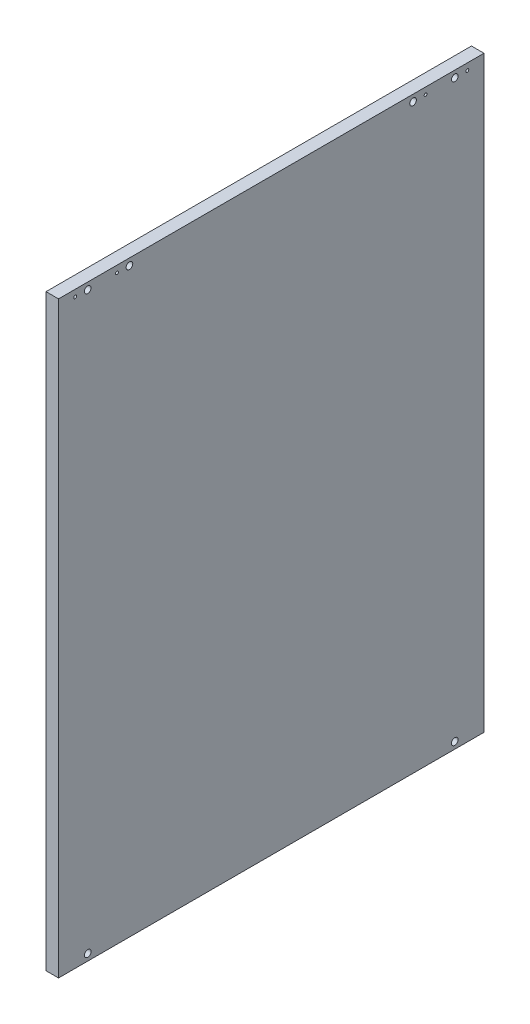
SolidWorks part; units mm, degrees
material "Pine"
ref_plane "Front Plane" through (0, 0, 0) normal (0, 0, 1) x (1, 0, 0)
ref_plane "Top Plane" through (0, 0, 0) normal (0, 1, 0) x (1, 0, 0)
ref_plane "Right Plane" through (0, 0, 0) normal (1, 0, 0) x (0, 0, -1)
sketch "Эскиз1" plane through (0, 0, 0) normal (1, 0, 0) x (0, 0, -1)
  line L1 (0, 0) -> (510, 0)
  line L2 (0, 0) -> (0, 705)
  line L3 (0, 705) -> (510, 705)
  line L4 (510, 0) -> (510, 705)
  dimension "D1" = 510
  dimension "D2" = 705
extrude "Вытянуть1" add sketch "Эскиз1" along normal blind 15
sketch "Шканты" plane through (15, 0, 0) normal (1, 0, 0) x (0, 0, -1)
  line L0 (0, 697) -> (510, 697) construction
  line L1 (0, 8) -> (510, 8) construction
  circle A0 centre (0, 0) radius 8 construction
  circle A1 centre (425, 697) radius 4
  circle A2 centre (510, 0) radius 8 construction
  circle A3 centre (475, 697) radius 4
  circle A4 centre (0, 8) radius 35 construction
  circle A5 centre (35, 697) radius 4
  circle A6 centre (510, 8) radius 35 construction
  circle A7 centre (85, 697) radius 4
  circle A8 centre (35, 8) radius 4
  circle A9 centre (475, 8) radius 4
  dimension "D1" = 8
  dimension "D2" = 8
  dimension "D3" = 35
  dimension "D6" = 70
  dimension "D4" = 70
  dimension "D7" = 8
  dimension "D8" = 8
  dimension "D9" = 8
  dimension "D10" = 8
  dimension "D5" = 85
extrude "Вырез-Вытянуть3" cut sketch "Шканты" against normal blind 10
sketch "Шурупы" plane through (15, 0, 0) normal (1, 0, 0) x (0, 0, -1)
  line L0 (0, 697) -> (510, 697) construction
  circle A0 centre (440, 697) radius 1.75
  circle A1 centre (490, 697) radius 1.75
  circle A3 centre (20, 697) radius 1.75
  circle A4 centre (70, 697) radius 1.75
  dimension "D1" = 8
  dimension "D2" = 20
  dimension "D3" = 70
extrude "Вырез-Вытянуть4" cut sketch "Шурупы" against normal blind 15
